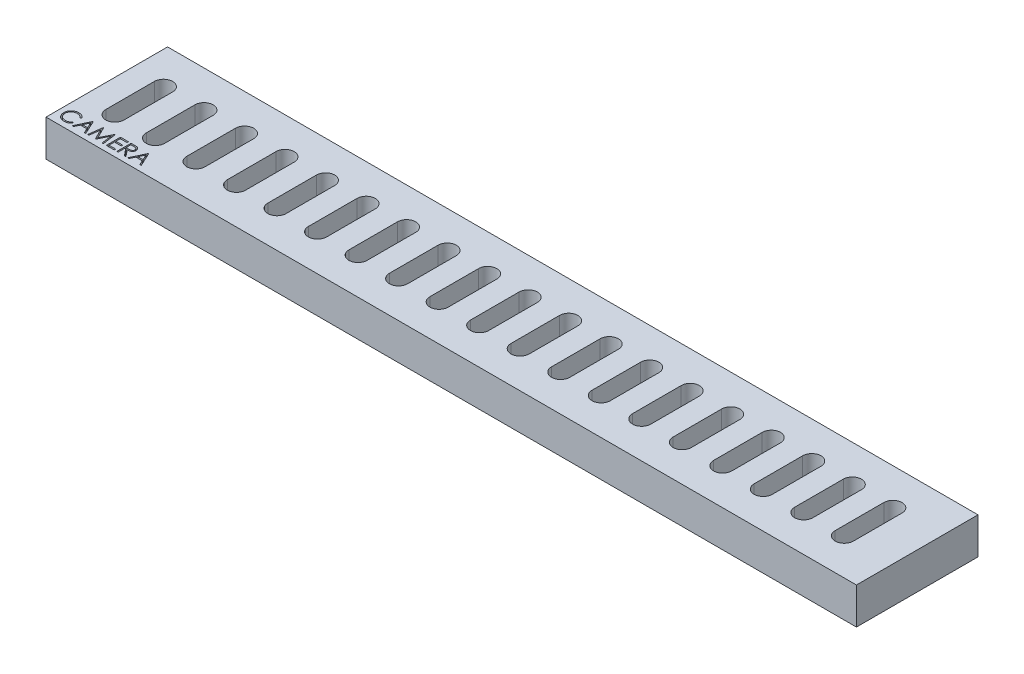
SolidWorks part; units mm, degrees
ref_plane "Front Plane" through (0, 0, 0) normal (0, 0, 1) x (1, 0, 0)
ref_plane "Top Plane" through (0, 0, 0) normal (0, 1, 0) x (1, 0, 0)
ref_plane "Right Plane" through (0, 0, 0) normal (1, 0, 0) x (0, 0, -1)
sketch "Sketch2" plane through (0, 0, 0) normal (0, 1, 0) x (1, 0, 0)
  line L1 (0, 0) -> (200, 0)
  line L2 (0, 0) -> (0, -30)
  line L3 (0, -30) -> (200, -30)
  line L4 (200, 0) -> (200, -30)
  dimension "D1" = 200
  dimension "D2" = 30
extrude "Boss-Extrude1" add sketch "Sketch2" along normal blind 9
sketch "Sketch3" plane through (0, 9, 0) normal (0, 1, 0) x (1, 0, 0)
  line L0 (8, 0) -> (8, -30) construction
  line L1 (200, 0) -> (0, 0) construction
  line L2 (0, -30) -> (200, -30) construction
  line L3 (18, 0) -> (18, -30) construction
  line L4 (18, -30) -> (28, -30) construction
  line L5 (28, -30) -> (28, 0) construction
  line L6 (28, 0) -> (38, 0) construction
  line L7 (38, 0) -> (38, -30) construction
  line L8 (38, -30) -> (48, -30) construction
  line L9 (48, -30) -> (48, 0) construction
  line L10 (48, 0) -> (58, 0) construction
  line L11 (58, 0) -> (58, -30) construction
  line L12 (58, -30) -> (68, -30) construction
  line L13 (68, -30) -> (68, 0) construction
  line L14 (68, 0) -> (78, 0) construction
  line L15 (78, 0) -> (78, -30) construction
  line L16 (0, 0) -> (0, -30) construction
  line L17 (88, 0) -> (88, -30) construction
  line L18 (88, -30) -> (108, -30) construction
  line L19 (98, -30) -> (98, 0) construction
  line L20 (108, 0) -> (108, -30) construction
  line L21 (118, 0) -> (118, -30) construction
  line L22 (128, 0) -> (118, 0) construction
  line L23 (128, -30) -> (128, 0) construction
  line L24 (138, -30) -> (128, -30) construction
  line L25 (138, 0) -> (138, -30) construction
  line L26 (148, 0) -> (138, 0) construction
  line L27 (148, -30) -> (148, 0) construction
  line L28 (158, -30) -> (148, -30) construction
  line L29 (158, 0) -> (158, -30) construction
  line L30 (168, 0) -> (158, 0) construction
  line L31 (168, -30) -> (168, 0) construction
  line L32 (178, -30) -> (168, -30) construction
  line L33 (178, 0) -> (178, -30) construction
  line L34 (188, 0) -> (188, -30) construction
  line L35 (0, -9) -> (200, -9) construction
  line L36 (200, -30) -> (200, 0) construction
  line L37 (200, -9) -> (200, -21) construction
  line L38 (200, -21) -> (0, -21) construction
  line L39 (8, -9) -> (8, -21) construction
  line L40 (10.25, -9) -> (10.25, -21)
  line L41 (5.75, -9) -> (5.75, -21)
  line L42 (18, -9) -> (18, -21) construction
  line L43 (20.25, -9) -> (20.25, -21)
  line L44 (15.75, -9) -> (15.75, -21)
  line L45 (28, -9) -> (28, -21) construction
  line L46 (30.25, -9) -> (30.25, -21)
  line L47 (25.75, -9) -> (25.75, -21)
  line L48 (38, -9) -> (38, -21) construction
  line L49 (40.25, -9) -> (40.25, -21)
  line L50 (35.75, -9) -> (35.75, -21)
  line L51 (48, -9) -> (48, -21) construction
  line L52 (50.25, -9) -> (50.25, -21)
  line L53 (45.75, -9) -> (45.75, -21)
  line L54 (58, -9) -> (58, -21) construction
  line L55 (60.25, -9) -> (60.25, -21)
  line L56 (55.75, -9) -> (55.75, -21)
  line L57 (68, -9) -> (68, -21) construction
  line L58 (70.25, -9) -> (70.25, -21)
  line L59 (65.75, -9) -> (65.75, -21)
  line L60 (78, -9) -> (78, -21) construction
  line L61 (80.25, -9) -> (80.25, -21)
  line L62 (75.75, -9) -> (75.75, -21)
  line L63 (88, -9) -> (88, -21) construction
  line L64 (90.25, -9) -> (90.25, -21)
  line L65 (85.75, -9) -> (85.75, -21)
  line L66 (98, -9) -> (98, -21) construction
  line L67 (100.25, -9) -> (100.25, -21)
  line L68 (95.75, -9) -> (95.75, -21)
  line L69 (108, -9) -> (108, -21) construction
  line L70 (110.25, -9) -> (110.25, -21)
  line L71 (105.75, -9) -> (105.75, -21)
  line L72 (118, -9) -> (118, -21) construction
  line L73 (120.25, -9) -> (120.25, -21)
  line L74 (115.75, -9) -> (115.75, -21)
  line L75 (128, -9) -> (128, -21) construction
  line L76 (130.25, -9) -> (130.25, -21)
  line L77 (125.75, -9) -> (125.75, -21)
  line L78 (138, -9) -> (138, -21) construction
  line L79 (140.25, -9) -> (140.25, -21)
  line L80 (135.75, -9) -> (135.75, -21)
  line L81 (148, -9) -> (148, -21) construction
  line L82 (150.25, -9) -> (150.25, -21)
  line L83 (145.75, -9) -> (145.75, -21)
  line L84 (158, -9) -> (158, -21) construction
  line L85 (160.25, -9) -> (160.25, -21)
  line L86 (155.75, -9) -> (155.75, -21)
  line L87 (168, -9) -> (168, -21) construction
  line L88 (170.25, -9) -> (170.25, -21)
  line L89 (165.75, -9) -> (165.75, -21)
  line L90 (178, -9) -> (178, -21) construction
  line L91 (180.25, -9) -> (180.25, -21)
  line L92 (175.75, -9) -> (175.75, -21)
  line L93 (188, -9) -> (188, -21) construction
  line L94 (190.25, -9) -> (190.25, -21)
  line L95 (185.75, -9) -> (185.75, -21)
  line L96 (8, -9) -> (18, -9) construction
  arc A0 (10.25, -9) -> (5.75, -9) centre (8, -9) ccw
  arc A1 (5.75, -21) -> (10.25, -21) centre (8, -21) ccw
  arc A2 (20.25, -9) -> (15.75, -9) centre (18, -9) ccw
  arc A3 (15.75, -21) -> (20.25, -21) centre (18, -21) ccw
  arc A4 (30.25, -9) -> (25.75, -9) centre (28, -9) ccw
  arc A5 (25.75, -21) -> (30.25, -21) centre (28, -21) ccw
  arc A6 (40.25, -9) -> (35.75, -9) centre (38, -9) ccw
  arc A7 (35.75, -21) -> (40.25, -21) centre (38, -21) ccw
  arc A8 (50.25, -9) -> (45.75, -9) centre (48, -9) ccw
  arc A9 (45.75, -21) -> (50.25, -21) centre (48, -21) ccw
  arc A10 (60.25, -9) -> (55.75, -9) centre (58, -9) ccw
  arc A11 (55.75, -21) -> (60.25, -21) centre (58, -21) ccw
  arc A12 (70.25, -9) -> (65.75, -9) centre (68, -9) ccw
  arc A13 (65.75, -21) -> (70.25, -21) centre (68, -21) ccw
  arc A14 (80.25, -9) -> (75.75, -9) centre (78, -9) ccw
  arc A15 (75.75, -21) -> (80.25, -21) centre (78, -21) ccw
  arc A16 (90.25, -9) -> (85.75, -9) centre (88, -9) ccw
  arc A17 (85.75, -21) -> (90.25, -21) centre (88, -21) ccw
  arc A18 (100.25, -9) -> (95.75, -9) centre (98, -9) ccw
  arc A19 (95.75, -21) -> (100.25, -21) centre (98, -21) ccw
  arc A20 (110.25, -9) -> (105.75, -9) centre (108, -9) ccw
  arc A21 (105.75, -21) -> (110.25, -21) centre (108, -21) ccw
  arc A22 (120.25, -9) -> (115.75, -9) centre (118, -9) ccw
  arc A23 (115.75, -21) -> (120.25, -21) centre (118, -21) ccw
  arc A24 (130.25, -9) -> (125.75, -9) centre (128, -9) ccw
  arc A25 (125.75, -21) -> (130.25, -21) centre (128, -21) ccw
  arc A26 (140.25, -9) -> (135.75, -9) centre (138, -9) ccw
  arc A27 (135.75, -21) -> (140.25, -21) centre (138, -21) ccw
  arc A28 (150.25, -9) -> (145.75, -9) centre (148, -9) ccw
  arc A29 (145.75, -21) -> (150.25, -21) centre (148, -21) ccw
  arc A30 (160.25, -9) -> (155.75, -9) centre (158, -9) ccw
  arc A31 (155.75, -21) -> (160.25, -21) centre (158, -21) ccw
  arc A32 (170.25, -9) -> (165.75, -9) centre (168, -9) ccw
  arc A33 (165.75, -21) -> (170.25, -21) centre (168, -21) ccw
  arc A34 (180.25, -9) -> (175.75, -9) centre (178, -9) ccw
  arc A35 (175.75, -21) -> (180.25, -21) centre (178, -21) ccw
  arc A36 (190.25, -9) -> (185.75, -9) centre (188, -9) ccw
  arc A37 (185.75, -21) -> (190.25, -21) centre (188, -21) ccw
  point P48 (0, -15)
  point P53 (8, -15)
  point P62 (18, -15)
  point P69 (28, -15)
  point P76 (38, -15)
  point P83 (48, -15)
  point P90 (58, -15)
  point P97 (68, -15)
  point P104 (78, -15)
  point P111 (88, -15)
  point P118 (98, -15)
  point P125 (108, -15)
  point P132 (118, -15)
  point P139 (128, -15)
  point P146 (138, -15)
  point P153 (148, -15)
  point P160 (158, -15)
  point P167 (168, -15)
  point P174 (178, -15)
  point P181 (188, -15)
  dimension "D1" = 8
  dimension "D2" = 10
  dimension "D3" = 10
  dimension "D4" = 10
  dimension "D5" = 10
  dimension "D6" = 10
  dimension "D7" = 10
  dimension "D8" = 10
  dimension "D9" = 10
  dimension "D10" = 10
  dimension "D11" = 6
  dimension "D12" = 6
  dimension "D14" = 10
  dimension "D15" = 4.5
  dimension "D13" = 19
extrude "Cut-Extrude1" cut sketch "Sketch3" against normal through all
sketch "Sketch4" plane through (0, 9, 0) normal (0, 1, 0) x (1, 0, 0)
  text T0 "CAMERA"
extrude "Cut-Extrude2" cut sketch "Sketch4" against normal blind 2.5
